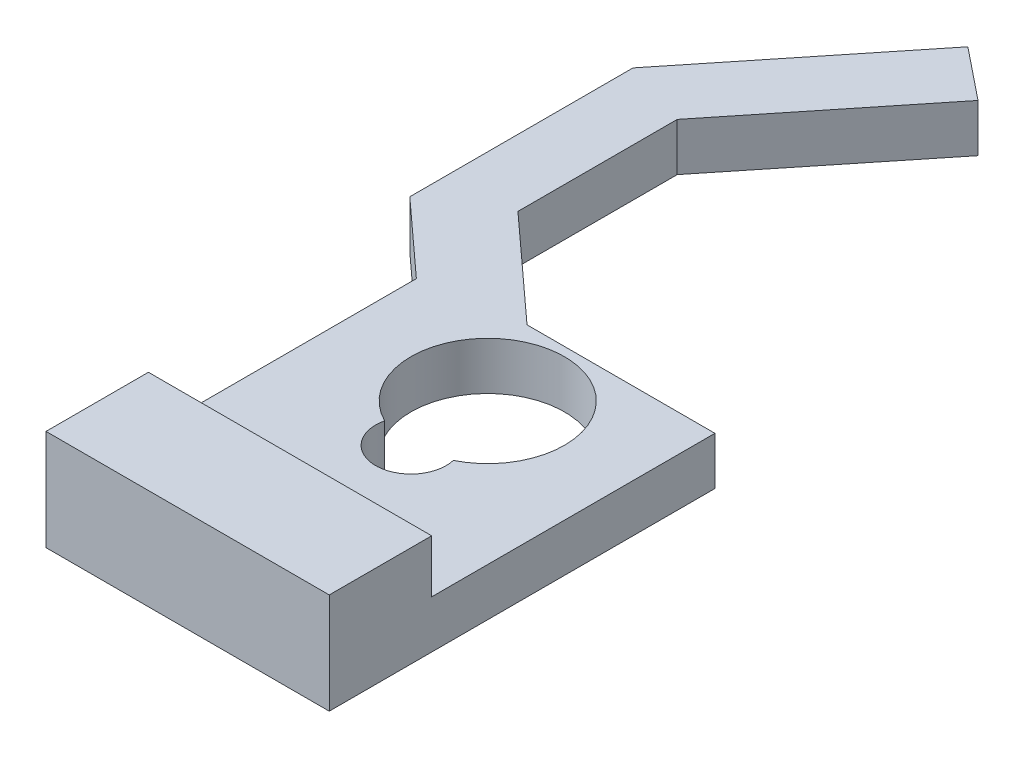
SolidWorks part; units mm, degrees
material "PVC Rígido"
ref_plane "Plano frontal" through (0, 0, 0) normal (0, 0, 1) x (1, 0, 0)
ref_plane "Plano superior" through (0, 0, 0) normal (0, 1, 0) x (1, 0, 0)
ref_plane "Plano direito" through (0, 0, 0) normal (1, 0, 0) x (0, 0, -1)
sketch "Esboço1" plane through (0, 0, 0) normal (0, 1, 0) x (1, 0, 0)
  line L0 (0, 0) -> (-14.05, 0) construction
  line L1 (-14.1591, 1.997) -> (-2.2091, 2.65)
  line L2 (-2.2091, -2.65) -> (-14.1591, -1.997)
  arc A0 (-2.2091, -2.65) -> (-2.2091, 2.65) centre (0, 0) ccw
  arc A1 (-14.1591, 1.997) -> (-14.1591, -1.997) centre (-14.05, 0) ccw
  dimension "D1" = 6.9
  dimension "D2" = 4
  dimension "D3" = 19.5
  dimension "D4" = 5.3
extrude "Ressalto-extrusão1" add sketch "Esboço1" against normal blind 1.4
sketch "Esboço2" plane through (0, -1.4, 0) normal (0, -1, 0) x (1, 0, 0)
  arc A0 (-2.2091, -2.65) -> (-2.2091, 2.65) centre (0, 0) ccw construction
  circle A1 centre (0, 0) radius 3.45
extrude "Ressalto-extrusão2" add sketch "Esboço2" along normal offset from surface (2.4 mm away) 3.8 up to face at (-7.242, 0, 0)
hole_wizard "Furo4" positions "Esboço9" profile "Esboço10" legacy end condition through all
sketch "Esboço9" plane through (0, 0, 0) normal (0, 1, 0) x (1, 0, 0)
  line L1 (-14.45, 0) -> (0, 0) construction
  arc A2 (-14.1591, 1.997) -> (-14.1591, -1.997) centre (-14.05, 0) ccw construction
  point P0 (-14.45, 0)
  point P19 (-16.05, 0)
  dimension "D1" = 1.6
sketch "Esboço10" plane through (-14.45, 0, 0) normal (1, 0, 0) x (0, 0, 1)
  line L0 (0, 0) -> (0, 3.8)
  line L1 (0, 3.8) -> (0.6, 3.8)
  line L2 (0.6, 3.8) -> (0.6, 0)
  line L3 (0.6, 0) -> (0, 0)
  line L4 (0, 110) -> (0, -10) construction
  dimension "Diameter" = 1.2
  dimension "Depth" = 3.8
pattern_linear "Padrão linear1" count 6 spacing 2 along (1, 0, 0) of "Furo4"
hole_wizard "Furo1" positions "Esboço3" profile "Esboço4" legacy
sketch "Esboço3" plane through (0, -3.8, 0) normal (0, -1, 0) x (-1, 0, 0)
  point P0 (0, 0)
sketch "Esboço4" plane through (0, -3.8, 0) normal (1, 0, 0) x (0, 0, -1)
  line L0 (0, 0) -> (0, 2)
  line L1 (0, 2) -> (2.475, 2)
  line L2 (2.475, 2) -> (2.475, 0)
  line L3 (2.475, 0) -> (0, 0)
  line L4 (0, 110) -> (0, -10) construction
  dimension "Diameter" = 4.95
  dimension "Depth" = 2
hole_wizard "Furo2" positions "Esboço5" profile "Esboço6" legacy
sketch "Esboço5" plane through (0, 0, 0) normal (0, 1, 0) x (1, 0, 0)
  point P0 (0, 0)
sketch "Esboço6" plane through (0, 0, 0) normal (1, 0, 0) x (0, 0, 1)
  line L0 (0, 0) -> (0, 1)
  line L1 (0, 1) -> (2.3, 1)
  line L2 (2.3, 1) -> (2.3, 0)
  line L3 (2.3, 0) -> (0, 0)
  line L4 (0, 110) -> (0, -10) construction
  dimension "Diameter" = 4.6
  dimension "Depth" = 1
hole_wizard "Furo3" positions "Esboço7" profile "Esboço8" legacy end condition through all
sketch "Esboço7" plane through (0, 0, 0) normal (0, 1, 0) x (1, 0, 0)
  point P0 (0, 0)
sketch "Esboço8" plane through (0, 0, 0) normal (1, 0, 0) x (0, 0, 1)
  line L0 (0, 0) -> (0, 3.8)
  line L1 (0, 3.8) -> (1.05, 3.8)
  line L2 (1.05, 3.8) -> (1.05, 0)
  line L3 (1.05, 0) -> (0, 0)
  line L4 (0, 110) -> (0, -10) construction
  dimension "Diameter" = 2.1
  dimension "Depth" = 3.8
sketch "Esboço11" plane through (0, -3.8, 0) normal (0, -1, 0) x (1, 0, 0)
  line L0 (-0.0981, 2.4731) -> (0, 2.375)
  line L1 (0, 2.375) -> (0.0981, 2.4731)
  line L2 (0, 0) -> (0, 2.475) construction
  circle A0 centre (0, 0) radius 2.375 construction
  circle A1 centre (0, 0) radius 2.475
  arc A2 (0.0981, 2.4731) -> (-0.0981, 2.4731) centre (0, 0) ccw
  dimension "D3" = 4.75
  dimension "D2" = 0.1
  dimension "D1" = 0
extrude "Ressalto-extrusão3" add sketch "Esboço11" against normal up to surface (2 mm away) up to face at (0, -1.8, 1.05)
pattern_circular "PadrãoCircular1" count 60 over 360 about axis through (0, 0, 0) along (0, 1, 0) of "Ressalto-extrusão3"
sketch "Sketch1" plane through (0, -3.8, 0) normal (0, -1, 0) x (1, 0, 0)
  line L0 (0, 3.45) -> (-16.05, 3.45)
  line L1 (-16.05, 3.45) -> (-16.05, -3.45)
  line L2 (-16.05, -3.45) -> (0, -3.45)
  arc A0 (0, 3.45) -> (0, -3.45) centre (0, 0) ccw
  circle A1 centre (0, 0) radius 3.45 construction
  arc A2 (-14.1591, 1.997) -> (-14.1591, -1.997) centre (-14.05, 0) ccw construction
  point P13 (-1.7998, -2.9434)
  point P14 (0, 0)
extrude "Cut-Extrude1" cut sketch "Sketch1" against normal blind 10
sketch "Sketch2" plane through (0, 0, 0) normal (0, 1, 0) x (1, 0, 0)
  line L0 (0, 3.45) -> (-11.8414, 14.241)
  line L1 (-11.8414, 14.241) -> (-11.8414, 26.8984)
  line L2 (-11.8414, 26.8984) -> (-1.2003, 40.1475)
  line L3 (-1.2003, 40.1475) -> (-5.2937, 43.4351)
  line L4 (-5.2937, 43.4351) -> (-17.1414, 28.6838)
  line L5 (-17.1414, 28.6838) -> (-17.1414, 10.9532)
  line L6 (-17.1414, 10.9532) -> (-2.3238, -2.55)
  circle A0 centre (0, 0) radius 3.45
  arc A1 (0, 3.45) -> (-2.3238, -2.55) centre (0, 0) ccw
  circle A2 centre (0, 0) radius 3.45 construction
  point P11 (-11.8414, 14.241)
  dimension "D1" = 17.7306
  dimension "D2" = 6
  dimension "D3" = 5.2502
  dimension "D4" = 5.3
  dimension "D5" = 141.23
  dimension "D6" = 20.0474
extrude "Boss-Extrude1" add sketch "Sketch2" against normal up to surface (3.8 mm away) contours L6 A1 L0 L1 L2 L3 L4 L5 up to face at (0, -3.8, 0)
sketch "Sketch4" plane through (0, -3.8, 0) normal (0, -1, 0) x (1, 0, 0)
  line L0 (3.8198, -4.756) -> (-3.8198, 4.756) construction
  line L1 (-17.1414, -28.6838) -> (-5.2937, -43.4351) construction
  line L3 (-11.25, -6.8) -> (11.25, -6.8)
  line L4 (-11.25, -6.8) -> (-11.25, 15.7)
  line L5 (-11.25, 15.7) -> (11.25, 15.7)
  line L6 (11.25, -6.8) -> (11.25, 15.7)
  circle A0 centre (0, 0) radius 6.1 construction
  circle A4 centre (0, 6.1) radius 2.8 construction
  point P13 (0, 0)
  point P14 (0, -6.8)
  dimension "D1" = 12.2
  dimension "D2" = 5.6
  dimension "D3" = 22.5
  dimension "D4" = 22.5
  dimension "D5" = 6.8
extrude "Boss-Extrude2" add sketch "Sketch4" against normal up to surface (3.8 mm away) up to face at (-7.8006, 0, -20.4454)
sketch "Sketch5" plane through (0, -3.8, 0) normal (0, -1, 0) x (1, 0, 0)
  circle A0 centre (0, 0) radius 6.1
  circle A1 centre (0, 6.1) radius 2.8
  dimension "D1" = 12.2
  dimension "D2" = 5.6
extrude "Cut-Extrude2" cut sketch "Sketch5" against normal blind 10 contours A0 | A1
sketch "Sketch6" plane through (0, -3.8, 0) normal (0, -1, 0) x (1, 0, 0)
  line L1 (-11.25, 23.836) -> (11.25, 23.836)
  line L2 (-11.25, 23.836) -> (-11.25, 15.7)
  line L3 (-11.25, 15.7) -> (11.25, 15.7)
  line L4 (11.25, 23.836) -> (11.25, 15.7)
  dimension "D1" = 8.136
extrude "Boss-Extrude3" add sketch "Sketch6" against normal blind 8
